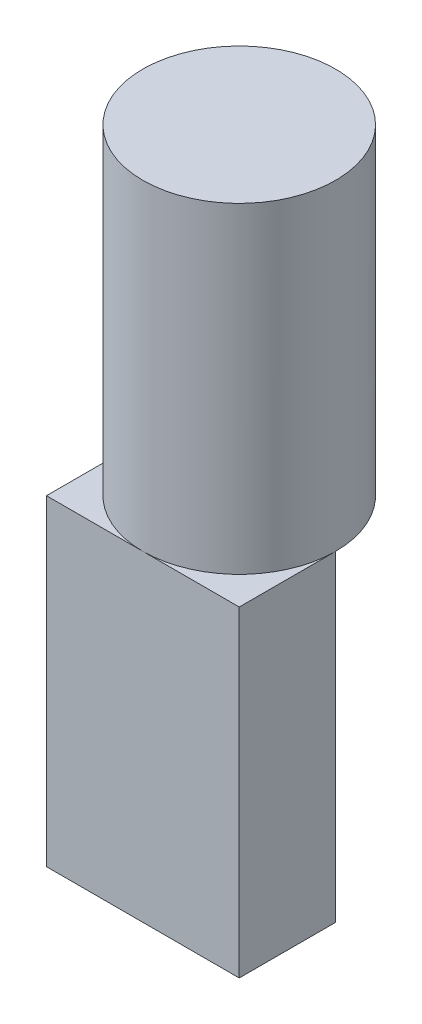
SolidWorks part; units mm, degrees
ref_plane "Plano frontal" through (0, 0, 0) normal (0, 0, 1) x (1, 0, 0)
ref_plane "Plano superior" through (0, 0, 0) normal (0, 1, 0) x (1, 0, 0)
ref_plane "Plano direito" through (0, 0, 0) normal (1, 0, 0) x (0, 0, -1)
sketch "Esboço1" plane through (0, 0, 0) normal (0, 1, 0) x (1, 0, 0)
  circle A0 centre (0, 0) radius 3
extrude "Ressalto-extrusão1" add sketch "Esboço1" along normal blind 10
sketch "Esboço2" plane through (0, 0, 0) normal (0, -1, 0) x (1, 0, 0)
  line L0 (-3, 0) -> (3, 0)
  line L1 (3, 0) -> (3, 3)
  line L2 (3, 3) -> (-3, 3)
  line L3 (-3, 3) -> (-3, 0)
  circle A0 centre (0, 0) radius 3 construction
  circle A1 centre (0, 0) radius 3 construction
extrude "Ressalto-extrusão2" add sketch "Esboço2" along normal blind 10
